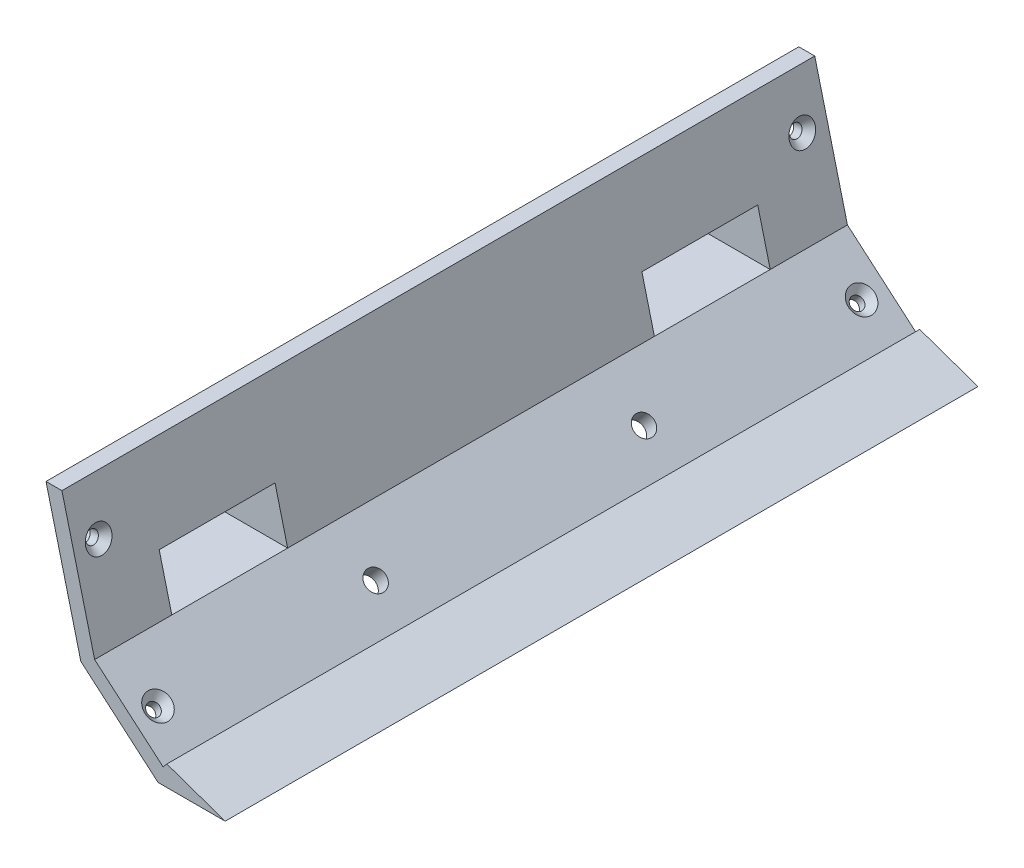
SolidWorks part; units mm, degrees
ref_plane "Alzado" through (0, 0, 0) normal (0, 0, 1) x (1, 0, 0)
ref_plane "Planta" through (0, 0, 0) normal (0, 1, 0) x (1, 0, 0)
ref_plane "Vista lateral" through (0, 0, 0) normal (1, 0, 0) x (0, 0, -1)
sketch "Croquis1" plane through (0, 0, 0) normal (0, 0, 1) x (1, 0, 0)
  line L0 (77.0085, 1.6467) -> (77.9847, 2.7856)
  line L1 (77.9847, 2.7856) -> (93.0864, -2.5)
  line L2 (93.0864, -2.5) -> (75.7, -2.5)
  line L3 (75.7, -2.5) -> (55.7, 14.6421)
  line L4 (55.7, 14.6421) -> (46.6759, 50.5119)
  line L5 (59.2688, 16.8514) -> (77.0085, 1.6467)
  line L8 (59.2688, 16.8514) -> (50.8006, 50.5119)
  line L9 (46.6759, 50.5119) -> (50.8006, 50.5119)
  dimension "D1" = 50.8006
  dimension "D3" = 59.2688
extrude "Saliente-Extruir1" add sketch "Croquis1" against normal up to vertex (195 mm away)
sketch "Croquis2" plane through (55.8489, 14.0503, 0) normal (-0.9698, -0.244, 0) x (0, 0, 1)
  circle A0 centre (-188.625, 23.7274) radius 1.625
  circle A1 centre (-6.375, 23.7274) radius 1.625
  dimension "D1" = 3.25
extrude "Cortar-Extruir1" cut sketch "Croquis2" against normal up to vertex (4 mm away)
sketch "Croquis3" plane through (30.8242, 35.9632, 0) normal (-0.6508, -0.7593, 0) x (0.7593, -0.6508, 0)
  circle A0 centre (47.2622, -188.625) radius 1.625
  circle A1 centre (47.2622, -6.375) radius 1.625
  dimension "D1" = 3.25
extrude "Cortar-Extruir2" cut sketch "Croquis3" against normal up to vertex (4 mm away)
sketch "Croquis4" plane through (33.4273, 39.0003, 0) normal (0.6508, 0.7593, 0) x (0.7593, -0.6508, 0)
  circle A0 centre (47.2622, 6.375) radius 3.36
  circle A1 centre (47.2622, 188.625) radius 3.36
  dimension "D1" = 6.7199
  dimension "D2" = 6.7199
extrude "Cortar-Extruir3" cut sketch "Croquis4" against normal blind 1.8 draft 44
sketch "Croquis5" plane through (59.728, 15.0262, 0) normal (0.9698, 0.244, 0) x (0, 0, -1)
  circle A0 centre (6.375, 23.7274) radius 3.36
  circle A1 centre (188.625, 23.7274) radius 3.36
  dimension "D1" = 6.7199
  dimension "D2" = 6.7199
extrude "Cortar-Extruir4" cut sketch "Croquis5" against normal blind 1.8 draft 44
ref_plane "Plano1" through (59.2688, 16.8514, -195) normal (0, 0, 1) x (1, 0, 0)
sketch "Croquis7" plane through (0, 0, -195) normal (0, 0, -1) x (-1, 0, 0)
  line L0 (-59.2688, 16.8514) -> (-55.1442, 16.8514) construction
  line L1 (-46.6759, 50.5119) -> (-55.7, 14.6421) construction
  line L3 (-59.2688, 16.8514) -> (-56.0313, 29.7201)
  line L4 (-59.2688, 16.8514) -> (-55.1442, 16.8514)
  line L6 (-56.0313, 29.7201) -> (-51.9067, 29.7201)
  line L8 (-59.2688, 16.8514) -> (-50.8006, 50.5119) construction
  line L9 (-55.1442, 16.8514) -> (-51.9067, 29.7201)
  dimension "D1" = 37.0551
extrude "Cortar-Extruir5" cut sketch "Croquis7" against normal blind 50
sketch "Croquis9" plane through (0, 0, 0) normal (0, 0, 1) x (1, 0, 0)
  line L0 (59.2688, 16.8514) -> (55.1442, 16.8514)
  line L1 (51.8737, 29.8514) -> (55.1442, 16.8514)
  line L2 (55.9983, 29.8514) -> (59.2688, 16.8514)
  line L3 (46.6759, 50.5119) -> (55.7, 14.6421) construction
  line L4 (51.8737, 29.8514) -> (55.9983, 29.8514)
  line L5 (59.2688, 16.8514) -> (50.8006, 50.5119) construction
  dimension "D1" = 21.0102
extrude "Cortar-Extruir6" cut sketch "Croquis9" against normal blind 50
sketch "Croquis10" plane through (0, 16.8514, 0) normal (0, 1, 0) x (1, 0, 0)
  line L0 (59.2688, 50) -> (39.8253, 50)
  line L1 (59.2688, 50) -> (59.2688, 0) construction
  line L2 (59.2688, 50) -> (59.2688, 20)
  line L3 (55.1442, 0) -> (59.2688, 0) construction
  line L4 (59.2688, 20) -> (39.8253, 20)
  line L6 (39.8253, 20) -> (39.8253, 50)
  line L7 (59.2688, 145) -> (39.8253, 145)
  line L13 (59.2688, 145) -> (59.2688, 175)
  line L15 (59.2688, 175) -> (39.8253, 175)
  line L16 (39.8253, 175) -> (39.8253, 145)
  dimension "D1" = 19.4435
  dimension "D2" = 20
  dimension "D3" = 50
  dimension "D4" = 145
extrude "Saliente-Extruir2" add sketch "Croquis10" against normal up to vertex (2.2094 mm away)
sketch "Croquis11" plane through (0, 29.7201, 0) normal (0, -1, 0) x (1, 0, 0)
  line L0 (56.0313, -145) -> (56.0313, -195) construction
  line L2 (56.0313, -145) -> (56.0313, -175)
  line L6 (56.0313, -145) -> (39.8253, -145)
  line L7 (39.8253, -145) -> (39.8253, -155.7)
  line L8 (39.8253, -175) -> (56.0313, -175)
  line L15 (39.8253, -155.7) -> (41.8753, -155.7)
  line L16 (37.1253, -155.7) -> (49.7253, -155.7) construction
  line L17 (41.8753, -155.7) -> (41.8753, -164.3)
  line L18 (41.8753, -164.3) -> (39.8253, -164.3)
  line L19 (39.8253, -164.3) -> (39.8253, -175)
  dimension "D1" = 14.156
extrude "Saliente-Extruir3" add sketch "Croquis11" against normal blind 2
sketch "Croquis12" plane through (0, 29.8514, 0) normal (0, -1, 0) x (1, 0, 0)
  line L2 (55.9983, -50) -> (55.9983, -20)
  line L6 (55.9983, -20) -> (39.8253, -20)
  line L7 (39.8253, -20) -> (39.8253, -30.7)
  line L8 (39.8253, -50) -> (55.9983, -50)
  line L9 (51.8737, -50) -> (51.8737, 0) construction
  line L15 (39.8253, -39.3) -> (41.8753, -39.3)
  line L16 (41.8753, -39.3) -> (41.8753, -30.7)
  line L17 (37.1253, -30.7) -> (49.7253, -30.7) construction
  line L18 (41.8753, -30.7) -> (39.8253, -30.7)
  line L19 (39.8253, -39.3) -> (39.8253, -50)
  dimension "D1" = 4.1246
  dimension "D2" = 9.9984
extrude "Saliente-Extruir4" add sketch "Croquis12" against normal blind 2
sketch "Croquis14" plane through (39.8253, 0, 0) normal (-1, 0, 0) x (0, 0, 1)
  line L0 (-137.75, 26.5514) -> (-137.75, 19.011)
  line L1 (-12.75, 26.5514) -> (-20, 31.8514)
  line L2 (-20, 31.8514) -> (-20, 14.6421)
  line L3 (-50, 16.8514) -> (-20, 16.8514) construction
  line L4 (-145, 31.7201) -> (-145, 14.6421)
  line L6 (-145, 14.6421) -> (-137.75, 19.011)
  line L7 (-12.75, 11.8804) -> (-12.75, 46.5119) construction
  line L8 (-12.75, 26.5514) -> (-12.75, 19.0514)
  line L9 (-12.75, 19.0514) -> (-20, 14.6421)
  line L10 (-57.25, 19.0514) -> (-57.25, 26.5514)
  line L11 (-57.25, 26.5514) -> (-50, 31.8514)
  line L12 (-50, 31.8514) -> (-50, 14.6421)
  line L13 (-50, 14.6421) -> (-57.25, 19.0514)
  line L15 (-137.75, 26.5514) -> (-145, 31.7201)
  line L16 (-182.25, 22.8014) -> (-182.25, 19.0514) construction
  line L17 (-182.25, 46.5119) -> (-182.25, 11.8804) construction
  line L18 (-182.25, 19.0514) -> (-175, 14.6421)
  line L19 (-175, 14.6421) -> (-175, 31.7201)
  line L20 (-175, 31.7201) -> (-182.25, 26.5514)
  line L21 (-182.25, 26.5514) -> (-182.25, 19.0514)
  arc A3 (-178.5, 26.5514) -> (-178.5, 19.0514) centre (-178.5, 22.8014) ccw construction
  dimension "D1" = 2.1595
  dimension "D2" = 7.5
  dimension "D3" = 7.5405
  dimension "D4" = 7.5
  dimension "D5" = 7.5
  dimension "D6" = 8.9807
  dimension "D7" = 8.4856
extrude "Saliente-Extruir5" add sketch "Croquis14" against normal up to vertex (16.206 mm away)
sketch "Croquis15" plane through (39.8253, 0, 0) normal (-1, 0, 0) x (0, 0, 1)
  line L0 (-182.25, 26.5514) -> (-181.0286, 27.4222)
  line L1 (-175, 31.7201) -> (-182.25, 26.5514) construction
  line L2 (-181.0286, 27.4222) -> (-181.0286, 18.3086)
  line L3 (-182.25, 19.0514) -> (-175, 14.6421) construction
  line L4 (-181.0286, 18.3086) -> (-182.25, 19.0514)
  line L5 (-182.25, 19.0514) -> (-182.25, 26.5514)
  line L6 (-12.75, 26.5514) -> (-13.9609, 27.4367)
  line L7 (-12.75, 26.5514) -> (-20, 31.8514) construction
  line L8 (-13.9609, 27.4367) -> (-13.9609, 18.315)
  line L9 (-20, 14.6421) -> (-12.75, 19.0514) construction
  line L10 (-13.9609, 18.315) -> (-12.75, 19.0514)
  line L11 (-12.75, 19.0514) -> (-12.75, 26.5514)
  dimension "D1" = 161.0391
extrude "Cortar-Extruir8" cut sketch "Croquis15" against normal up to vertex
sketch "Croquis16" plane through (39.8253, 0, 0) normal (-1, 0, 0) x (0, 0, 1)
  circle A0 centre (-53.5, 22.8014) radius 1.6
  circle A1 centre (-16.5, 22.8014) radius 1.6
  circle A2 centre (-178.5, 22.8014) radius 1.6
  circle A3 centre (-141.5, 22.8014) radius 1.6
  dimension "D1" = 3.2
extrude "Cortar-Extruir9" cut sketch "Croquis16" against normal blind 4
sketch "Croquis17" plane through (0, 0, 0) normal (0, 0, 1) x (1, 0, 0)
  line L0 (51.8737, 29.8514) -> (55.9983, 29.8514)
  line L1 (55.9983, 29.8514) -> (59.2688, 16.8514)
  line L2 (59.2688, 16.8514) -> (55.1442, 16.8514)
  line L3 (55.1442, 16.8514) -> (51.8737, 29.8514)
extrude "Saliente-Extruir6" add sketch "Croquis17" against normal up to vertex
sketch "Croquis18" plane through (0, 0, -195) normal (0, 0, -1) x (-1, 0, 0)
  line L0 (-59.2688, 16.8514) -> (-55.1442, 16.8514)
  line L1 (-55.1442, 16.8514) -> (-51.9067, 29.7201)
  line L2 (-51.9067, 29.7201) -> (-56.0313, 29.7201)
  line L3 (-56.0313, 29.7201) -> (-59.2688, 16.8514)
extrude "Saliente-Extruir7" add sketch "Croquis18" against normal up to vertex
sketch "Croquis19" plane through (33.4273, 39.0003, 0) normal (0.6508, 0.7593, 0) x (0.7593, -0.6508, 0)
  line L0 (34.0346, 50) -> (34.0346, 62.75) construction
  line L1 (34.0346, 145) -> (34.0346, 50) construction
  line L2 (34.0346, 145) -> (34.0346, 132.25) construction
  line L4 (47.2622, 6.375) -> (47.2622, 62.75) construction
  line L5 (34.0346, 132.25) -> (47.2622, 132.25) construction
  line L6 (57.3987, 195) -> (57.3987, 0) construction
  circle A0 centre (47.2622, 62.75) radius 2.625
  circle A1 centre (47.2622, 132.25) radius 2.625
  dimension "D1" = 5.25
  dimension "D2" = 62.75
extrude "Cortar-Extruir10" cut sketch "Croquis19" against normal up to vertex (4 mm away) up to point (75.7, -2.5, 0)
sketch "Croquis20" plane through (0, 0, -195) normal (0, 0, -1) x (-1, 0, 0)
  line L0 (-56.0313, 29.7201) -> (-56.0313, 31.8514)
  line L1 (-56.0313, 31.8514) -> (-55.4951, 31.8514)
  line L2 (-55.4951, 31.8514) -> (-56.0313, 29.7201)
extrude "Cortar-Extruir11" cut sketch "Croquis20" against normal up to vertex
